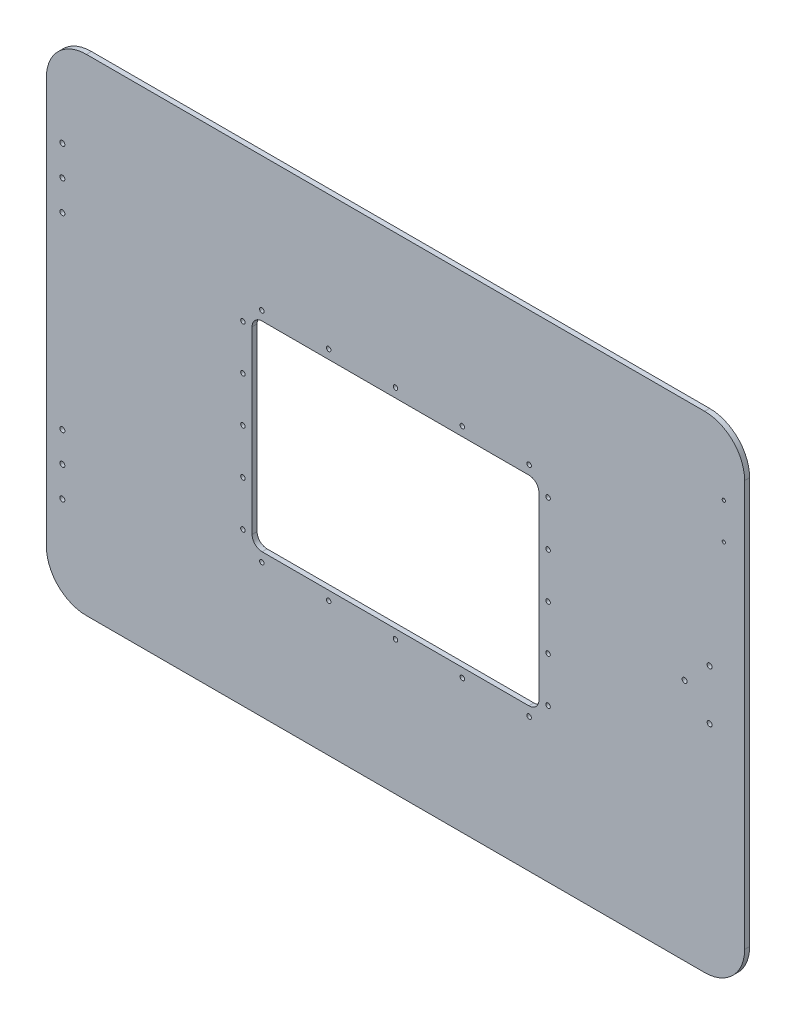
SolidWorks part; units mm, degrees
material "3.3315 (EN-AW 5005)"
ref_plane "Front Plane" through (0, 0, 0) normal (0, 0, 1) x (1, 0, 0)
ref_plane "Top Plane" through (0, 0, 0) normal (0, 1, 0) x (1, 0, 0)
ref_plane "Right Plane" through (0, 0, 0) normal (1, 0, 0) x (0, 0, -1)
sketch "Sketch1" plane through (0, 0, 0) normal (0, 0, 1) x (1, 0, 0)
  line L0 (308, 231.95) -> (-308, 231.95) construction
  line L1 (349, -242.95) -> (-349, -242.95)
  line L2 (349, -242.95) -> (349, 242.95)
  line L3 (349, 242.95) -> (-349, 242.95)
  line L4 (-349, -242.95) -> (-349, 242.95)
  line L5 (349, -242.95) -> (-349, 242.95) construction
  line L6 (349, 242.95) -> (-349, -242.95) construction
  line L7 (338, -201.95) -> (338, 201.95) construction
  point P0 (0, 0)
  dimension "D1" = 11
  dimension "D2" = 11
extrude "Boss-Extrude1" add sketch "Sketch1" along normal blind 5
fillet "Fillet1" radius 40 4 edges at (-349, 242.95, 2.5) (-349, -242.95, 2.5) (349, -242.95, 2.5) (349, 242.95, 2.5)
hole_wizard "M6 Tapped Hole1" positions "Sketch2" profile "Sketch3" tap size "M6" standard "ISO" end condition through all
sketch "Sketch2" plane through (0, 0, 5) normal (0, 0, 1) x (1, 0, 0)
  point P0 (-333, 153.95)
  point P3 (-333, 123.95)
  point P6 (-333, 93.95)
sketch "Sketch3" plane through (-333, 153.95, 5) normal (1, 0, 0) x (0, -1, 0)
  line L0 (0, 0) -> (0, 5)
  line L1 (0, 5) -> (2.5, 5)
  line L2 (2.5, 5) -> (2.5, 0)
  line L5 (2.5, 0) -> (0, 0)
  line L11 (0, -6.35) -> (0, 107.95) construction
  dimension "Thread Major Dia." = 5
  dimension "Thru Tap Drill Depth" = 5
hole_wizard "M6 Tapped Hole2" positions "Sketch4" profile "Sketch5" tap size "M6" standard "ISO" end condition through all
sketch "Sketch4" plane through (0, 0, 5) normal (0, 0, 1) x (1, 0, 0)
  point P0 (314, 25)
  point P3 (289, 0)
  point P6 (314, -25)
sketch "Sketch5" plane through (314, 25, 5) normal (1, 0, 0) x (0, -1, 0)
  line L0 (0, 0) -> (0, 5)
  line L1 (0, 5) -> (2.5, 5)
  line L2 (2.5, 5) -> (2.5, 0)
  line L5 (2.5, 0) -> (0, 0)
  line L11 (0, -6.35) -> (0, 107.95) construction
  dimension "Thread Major Dia." = 5
  dimension "Thru Tap Drill Depth" = 5
mirror "Mirror1" about plane through (0, 0, 0) normal (0, 1, 0) of "M6 Tapped Hole1"
hole_wizard "M4 Tapped Hole1" positions "Sketch6" profile "Sketch7" tap size "M4" standard "ISO" end condition through all
sketch "Sketch6" plane through (0, 0, 5) normal (0, 0, 1) x (1, 0, 0)
  point P0 (328.1806, 175.459)
  point P3 (328.1806, 139.459)
sketch "Sketch7" plane through (328.1806, 175.459, 5) normal (1, 0, 0) x (0, -1, 0)
  line L0 (0, 0) -> (0, 5)
  line L1 (0, 5) -> (1.65, 5)
  line L2 (1.65, 5) -> (1.65, 0)
  line L5 (1.65, 0) -> (0, 0)
  line L11 (0, -6.35) -> (0, 107.95) construction
  dimension "Thru Tap Drill Dia." = 3.3
  dimension "Thru Tap Drill Depth" = 5
cosmetic thread "Hole Thread1" parameters "D2"=4
cosmetic thread "Hole Thread2" parameters "D2"=4
sketch "Sketch8" plane through (0, 0, 5) normal (0, 0, 1) x (1, 0, 0)
  line L0 (-143.35, -99.85) -> (-143.35, 99.85)
  line L1 (-148.5, -105) -> (148.5, -105) construction
  line L2 (-148.5, -105) -> (-148.5, 105) construction
  line L3 (-148.5, 105) -> (148.5, 105) construction
  line L4 (148.5, -105) -> (148.5, 105) construction
  line L5 (-148.5, -105) -> (148.5, 105) construction
  line L6 (-148.5, 105) -> (148.5, -105) construction
  line L7 (-143.35, 99.85) -> (143.35, 99.85)
  line L8 (143.35, -99.85) -> (143.35, 99.85)
  line L9 (-143.35, -99.85) -> (143.35, -99.85)
  point P0 (0, 0)
  dimension "D1" = 297
  dimension "D2" = 210
  dimension "D3" = 5.15
extrude "Cut-Extrude1" cut sketch "Sketch8" against normal through all
fillet "Fillet2" radius 10 4 edges at (143.35, 99.85, 2.5) (143.35, -99.85, 2.5) (-143.35, -99.85, 2.5) (-143.35, 99.85, 2.5)
sketch "Sketch9" plane through (0, 0, 5) normal (0, 0, 1) x (1, 0, 0)
  line L0 (-133.35, -99.85) -> (133.35, -99.85) construction
  line L1 (143.35, -89.85) -> (143.35, 89.85) construction
  line L2 (133.35, 99.85) -> (-133.35, 99.85) construction
  line L3 (-143.35, 89.85) -> (-143.35, -89.85) construction
  line L4 (-133.35, -99.85) -> (133.35, -99.85)
  line L5 (143.35, -89.85) -> (143.35, 89.85)
  line L6 (133.35, 99.85) -> (-133.35, 99.85)
  line L7 (-143.35, 89.85) -> (-143.35, -89.85)
  arc A0 (-143.35, -89.85) -> (-133.35, -99.85) centre (-133.35, -89.85) ccw construction
  arc A1 (133.35, -99.85) -> (143.35, -89.85) centre (133.35, -89.85) ccw construction
  arc A2 (143.35, 89.85) -> (133.35, 99.85) centre (133.35, 89.85) ccw construction
  arc A3 (-133.35, 99.85) -> (-143.35, 89.85) centre (-133.35, 89.85) ccw construction
  arc A4 (-143.35, -89.85) -> (-133.35, -99.85) centre (-133.35, -89.85) ccw
  arc A5 (133.35, -99.85) -> (143.35, -89.85) centre (133.35, -89.85) ccw
  arc A6 (143.35, 89.85) -> (133.35, 99.85) centre (133.35, 89.85) ccw
  arc A7 (-133.35, 99.85) -> (-143.35, 89.85) centre (-133.35, 89.85) ccw
hole_wizard "M4 Clearance Hole1" positions "Sketch10" profile "Sketch11" hole size "M4" standard "ISO" end condition through all
sketch "Sketch10" plane through (0, 0, 5) normal (0, 0, 1) x (1, 0, 0)
  point P1 (152.5, 90.1)
  point P4 (152.5, 45.05)
  point P7 (133.6, 109)
  point P10 (66.8, 109)
  point P13 (0, 109)
  point P16 (-66.8, 109)
  point P19 (-133.6, 109)
  point P22 (-152.5, 90.1)
  point P25 (-152.5, 45.05)
  point P28 (-152.5, 0)
  point P31 (-152.5, -45.05)
  point P34 (-152.5, -90.1)
  point P37 (-133.6, -109)
  point P40 (-66.8, -109)
  point P43 (0, -109)
  point P46 (66.8, -109)
  point P49 (133.6, -109)
  point P52 (152.5, -90.1)
  point P55 (152.5, -45.05)
  point P58 (152.5, 0)
sketch "Sketch11" plane through (152.5, 90.1, 5) normal (1, 0, 0) x (0, -1, 0)
  line L0 (0, 0) -> (0, 5)
  line L1 (0, 5) -> (2.25, 5)
  line L2 (2.25, 5) -> (2.25, 0)
  line L5 (2.25, 0) -> (0, 0)
  line L11 (0, -6.35) -> (0, 107.95) construction
  dimension "Thru Hole Dia." = 4.5
  dimension "Thru Hole Depth" = 5
